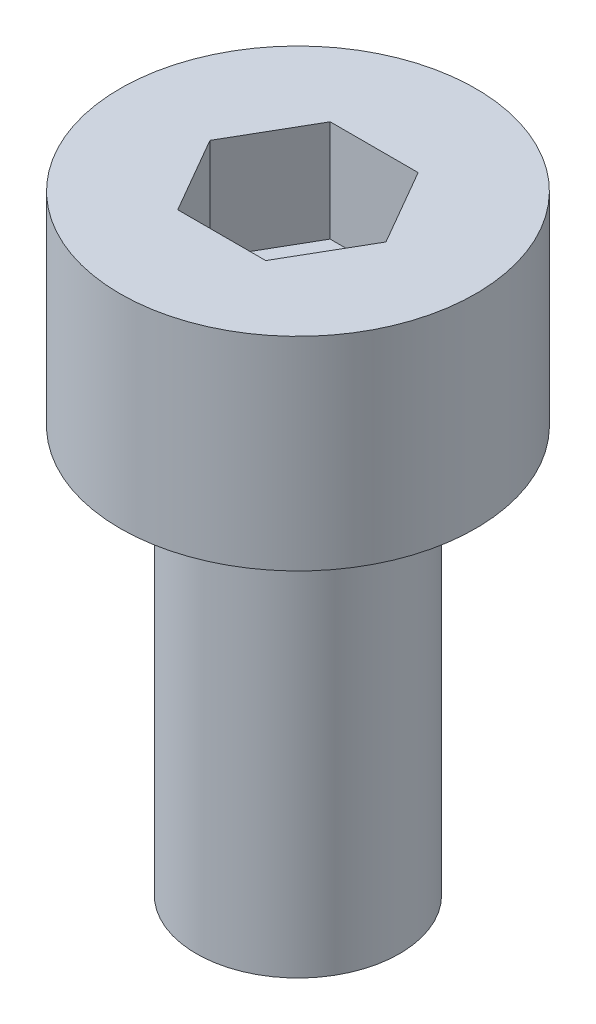
SolidWorks part; units mm, degrees
material "AISI 304"
ref_plane "前视基准面" through (0, 0, 0) normal (0, 0, 1) x (1, 0, 0)
ref_plane "上视基准面" through (0, 0, 0) normal (0, 1, 0) x (1, 0, 0)
ref_plane "右视基准面" through (0, 0, 0) normal (1, 0, 0) x (0, 0, -1)
sketch "草图1" plane through (0, 0, 0) normal (0, 1, 0) x (1, 0, 0)
  circle A0 centre (0, 0) radius 3.5
  dimension "D1" = 7
extrude "杯头" add sketch "草图1" along normal blind 4
sketch "草图2" plane through (0, 4, 0) normal (0, 1, 0) x (1, 0, 0)
  line L1 (1.7321, 0) -> (0.866, 1.5)
  line L2 (0.866, 1.5) -> (-0.866, 1.5)
  line L3 (-0.866, 1.5) -> (-1.7321, 0)
  line L4 (-1.7321, 0) -> (-0.866, -1.5)
  line L5 (-0.866, -1.5) -> (0.866, -1.5)
  line L6 (0.866, -1.5) -> (1.7321, 0)
  circle A0 centre (0, 0) radius 1.5 construction
  dimension "D1" = 3
extrude "内六角口" cut sketch "草图2" against normal blind 2
sketch "草图3" plane through (0, 0, 0) normal (0, -1, 0) x (1, 0, 0)
  circle A0 centre (0, 0) radius 2
  dimension "D1" = 4
extrude "螺纹长度" add sketch "草图3" along normal blind 8
